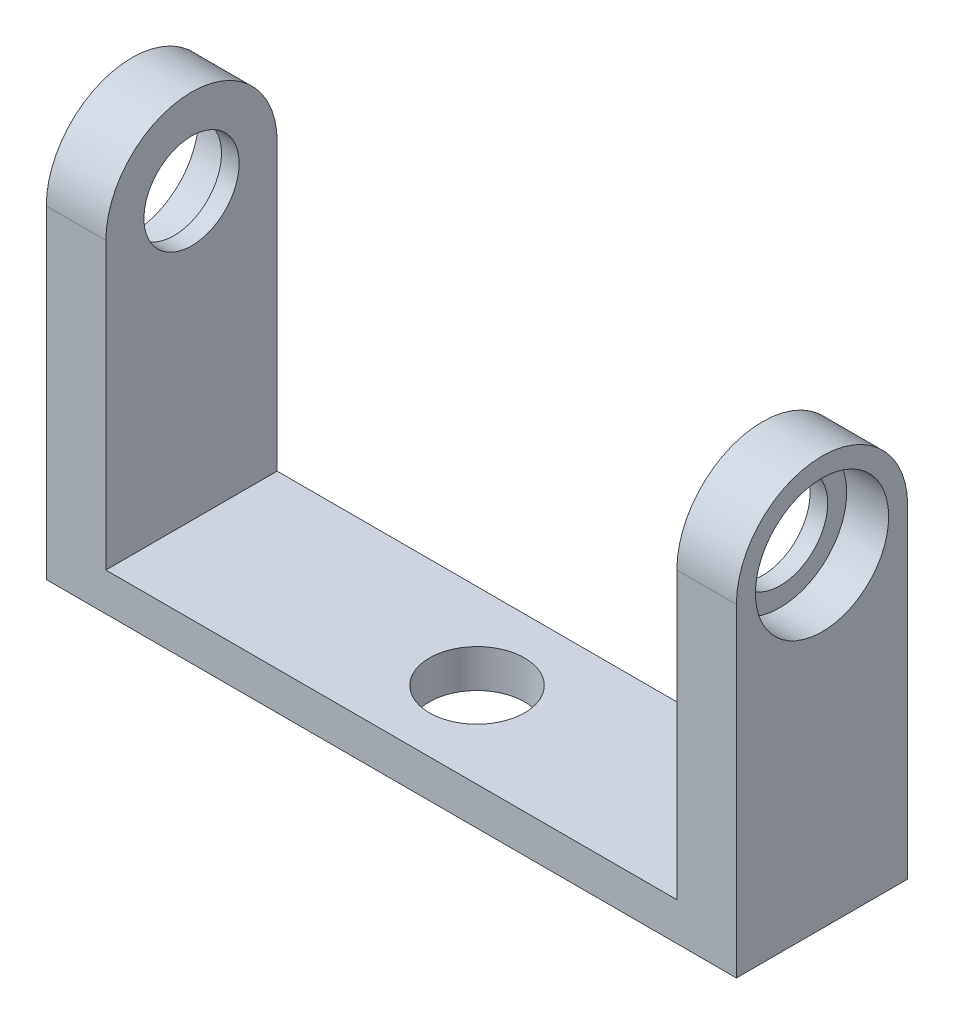
SolidWorks part; units mm, degrees
ref_plane "Front" through (0, 0, 0) normal (0, 0, 1) x (1, 0, 0)
ref_plane "Top" through (0, 0, 0) normal (0, 1, 0) x (1, 0, 0)
ref_plane "Right" through (0, 0, 0) normal (1, 0, 0) x (0, 0, -1)
sketch "Sketch1" plane through (0, 0, 0) normal (1, 0, 0) x (0, 0, -1)
  circle A0 centre (0, 0) radius 9
  circle A1 centre (0, 0) radius 5
  dimension "D1" = 10
  dimension "D2" = 18
extrude "Boss-Extrude1" add sketch "Sketch1" along normal blind 6.26
sketch "Sketch3" plane through (0, 0, 0) normal (-1, 0, 0) x (0, 0, 1)
  line L0 (-9, 0) -> (-9, -30)
  line L1 (-9, -30) -> (9, -30)
  line L2 (9, -30) -> (9, 0)
  line L3 (-9, 0) -> (9, 0) construction
  line L5 (-9, 0) -> (-5, 0)
  line L6 (5, 0) -> (9, 0)
  circle A0 centre (0, 0) radius 9 construction
  arc A1 (-5, 0) -> (5, 0) centre (0, 0) ccw
  circle A2 centre (0, 0) radius 5 construction
  point P10 (-9, 0)
  dimension "D1" = 30
extrude "Boss-Extrude2" add sketch "Sketch3" against normal up to surface (6.26 mm away) up to face at (6.26, 0, -9)
sketch "Sketch2" plane through (6.26, 0, 0) normal (1, 0, 0) x (0, 0, -1)
  circle A0 centre (0, 0) radius 7
  dimension "D1" = 14
extrude "Cut-Extrude1" cut sketch "Sketch2" against normal blind 4.41
sketch "Sketch4" plane through (0, -30, 0) normal (0, -1, 0) x (1, 0, 0)
  line L0 (6.26, -9) -> (6.26, 9) construction
  line L1 (6.26, 9) -> (-30, 9)
  line L2 (6.26, 9) -> (6.26, -9)
  line L3 (6.26, -9) -> (-30, -9)
  line L4 (-30, 9) -> (-30, -9)
  point P6 (6.26, 0)
  point P7 (6.26, 0)
  point P8 (6.26, 0)
  dimension "D1" = 36.26
  dimension "D2" = 18
extrude "Boss-Extrude3" add sketch "Sketch4" along normal blind 4
ref_plane "Plane1" through (-30, 0, 0) normal (-1, 0, 0) x (0, 0, 1)
mirror "Mirror2" about plane through (-30, -34, 9) normal (1, 0, 0) of bodies 104
sketch "Sketch5" plane through (0, -30, 0) normal (0, 1, 0) x (1, 0, 0)
  line L0 (-60, 9) -> (0, 9) construction
  line L1 (-30, 9) -> (-30, -9) construction
  line L2 (0, -9) -> (-60, -9) construction
  circle A0 centre (-30, 0) radius 5
  point P0 (-30, 9)
  dimension "D1" = 10
extrude "Cut-Extrude2" cut sketch "Sketch5" against normal through all
